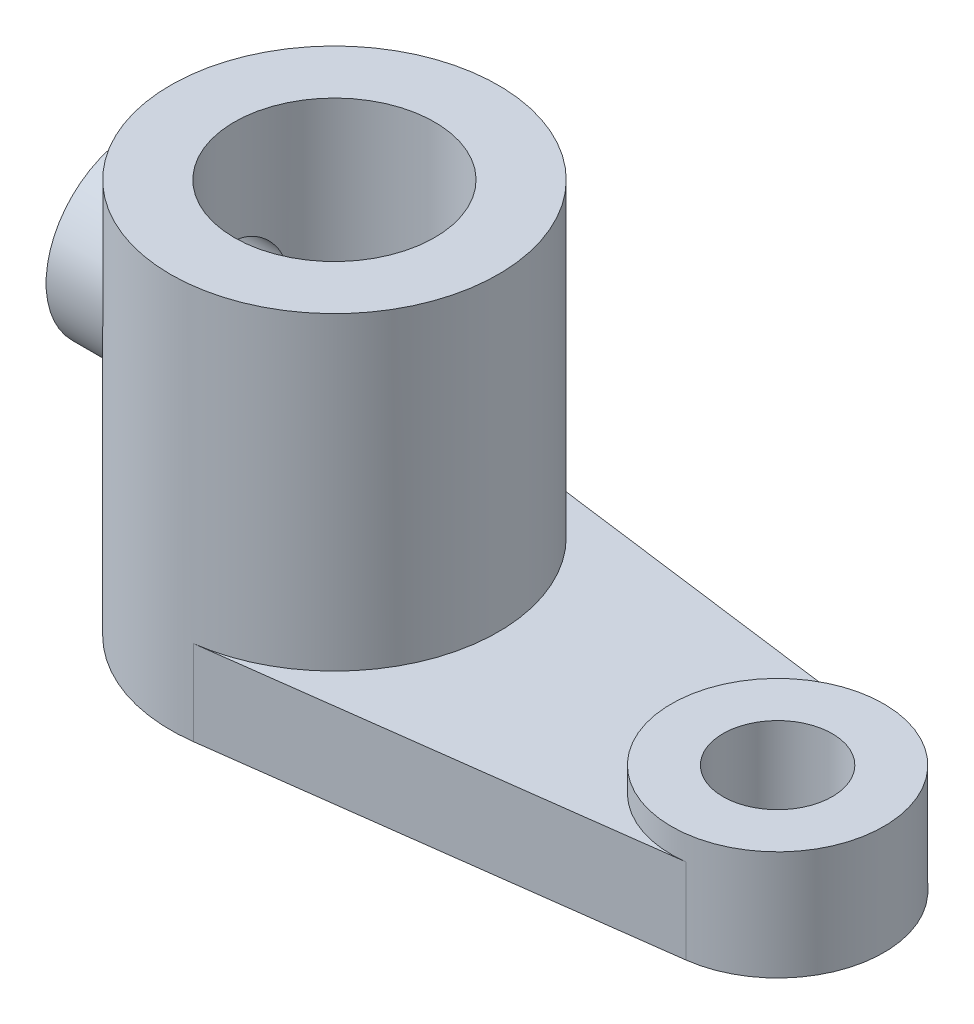
SolidWorks part; units mm, degrees
ref_plane "前视基准面" through (0, 0, 0) normal (0, 0, 1) x (1, 0, 0)
ref_plane "上视基准面" through (0, 0, 0) normal (0, 1, 0) x (1, 0, 0)
ref_plane "右视基准面" through (0, 0, 0) normal (1, 0, 0) x (0, 0, -1)
sketch "草图1" plane through (0, 0, 0) normal (0, 1, 0) x (1, 0, 0)
  line L0 (-55, 0) -> (55, 0) construction
  line L1 (0, -55) -> (0, 55) construction
  line L2 (3.5137, -26.7704) -> (75.2774, -17.3512)
  line L3 (3.5137, 26.7704) -> (75.2774, 17.3512)
  arc A0 (3.5137, 26.7704) -> (3.5137, -26.7704) centre (0, 0) ccw
  arc A1 (75.2774, -17.3512) -> (75.2774, 17.3512) centre (73, 0) ccw
  dimension "D1" = 54
  dimension "D2" = 0
  dimension "D3" = 73
  dimension "D4" = 35
extrude "凸台-拉伸1" add sketch "草图1" along normal blind 14
sketch "草图2" plane through (0, 0, 0) normal (0, 1, 0) x (1, 0, 0)
  circle A0 centre (0, 0) radius 27
extrude "凸台-拉伸2" add sketch "草图2" along normal blind 65 contours A0
sketch "草图3" plane through (0, 0, 0) normal (0, 1, 0) x (1, 0, 0)
  line L0 (-35.75, 0) -> (35.75, 0) construction
  circle A0 centre (73, 0) radius 17.5
  arc A1 (75.2774, -17.3512) -> (75.2774, 17.3512) centre (73, 0) ccw construction
extrude "凸台-拉伸3" add sketch "草图3" along normal blind 18
sketch "草图4" plane through (0, 0, 0) normal (1, 0, 0) x (0, 0, -1)
  line L0 (0, 35.75) -> (0, -35.75) construction
  line L1 (29.7, 0) -> (-29.7, 0) construction
  circle A0 centre (0, 41) radius 14.5
  dimension "D1" = 29
  dimension "D2" = 41
extrude "凸台-拉伸4" add sketch "草图4" against normal blind 33
sketch "草图5" plane through (0, 65, 0) normal (0, 1, 0) x (1, 0, 0)
  circle A0 centre (0, 0) radius 16.5
extrude "切除-拉伸1" cut sketch "草图5" against normal through all
sketch "草图6" plane through (0, 18, 0) normal (0, 1, 0) x (1, 0, 0)
  circle A0 centre (73, 0) radius 9
extrude "切除-拉伸2" cut sketch "草图6" against normal through all
sketch "草图7" plane through (-33, 0, 0) normal (-1, 0, 0) x (0, 0, 1)
  line L0 (0, -35.75) -> (0, 35.75) construction
  circle A0 centre (0, 41) radius 7
  circle A1 centre (0, 41) radius 14.5 construction
extrude "切除-拉伸3" cut sketch "草图7" against normal blind 33
